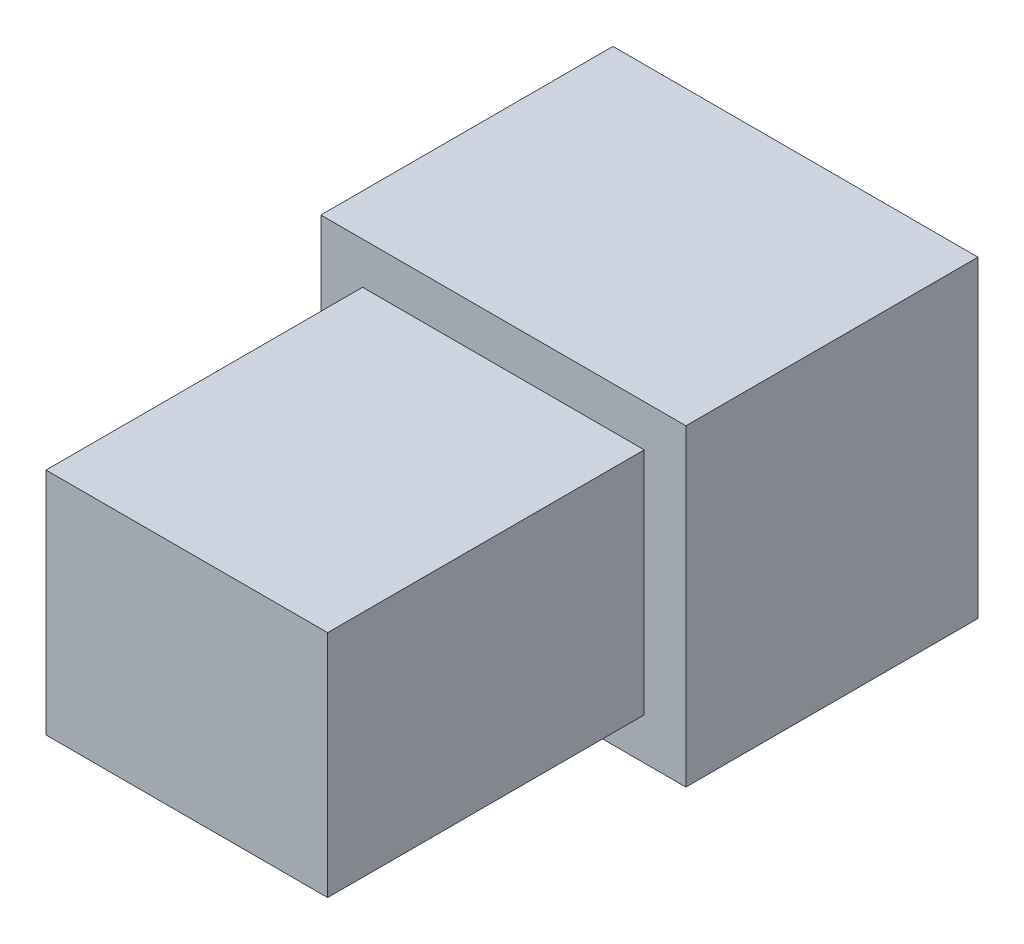
SolidWorks part; units mm, degrees
ref_plane "Front Plane" through (0, 0, 0) normal (0, 0, 1) x (1, 0, 0)
ref_plane "Top Plane" through (0, 0, 0) normal (0, 1, 0) x (1, 0, 0)
ref_plane "Right Plane" through (0, 0, 0) normal (1, 0, 0) x (0, 0, -1)
sketch "Sketch1" plane through (0, 0, 0) normal (0, 0, 1) x (1, 0, 0)
  line L0 (3860.75, -250) -> (-2612.75, -250) construction
  line L1 (4124, -1750) -> (7624, -1750)
  line L2 (4124, -1750) -> (4124, 1250)
  line L3 (4124, 1250) -> (7624, 1250)
  line L4 (7624, -1750) -> (7624, 1250)
  line L5 (624, -3938.7401) -> (624, 3438.7401) construction
  dimension "D1" = 1500
  dimension "D2" = 3000
  dimension "D3" = 3500
  dimension "D4" = 3500
extrude "Extrude1" add sketch "Sketch1" along normal blind 2800
sketch "Sketch3" plane through (0, 0, 2800) normal (0, 0, 1) x (1, 0, 0)
  line L8 (4524, 850) -> (4524, -1350)
  line L9 (4524, -1350) -> (7224, -1350)
  line L10 (7224, -1350) -> (7224, 850)
  line L11 (7224, 850) -> (4524, 850)
  line L12 (4524, 850) -> (4524, -1350)
  line L13 (4524, -1350) -> (7224, -1350)
  line L14 (7224, -1350) -> (7224, 850)
  line L15 (7224, 850) -> (4524, 850)
  dimension "D1" = 400
extrude "Extrude2" add sketch "Sketch3" along normal blind 3035
